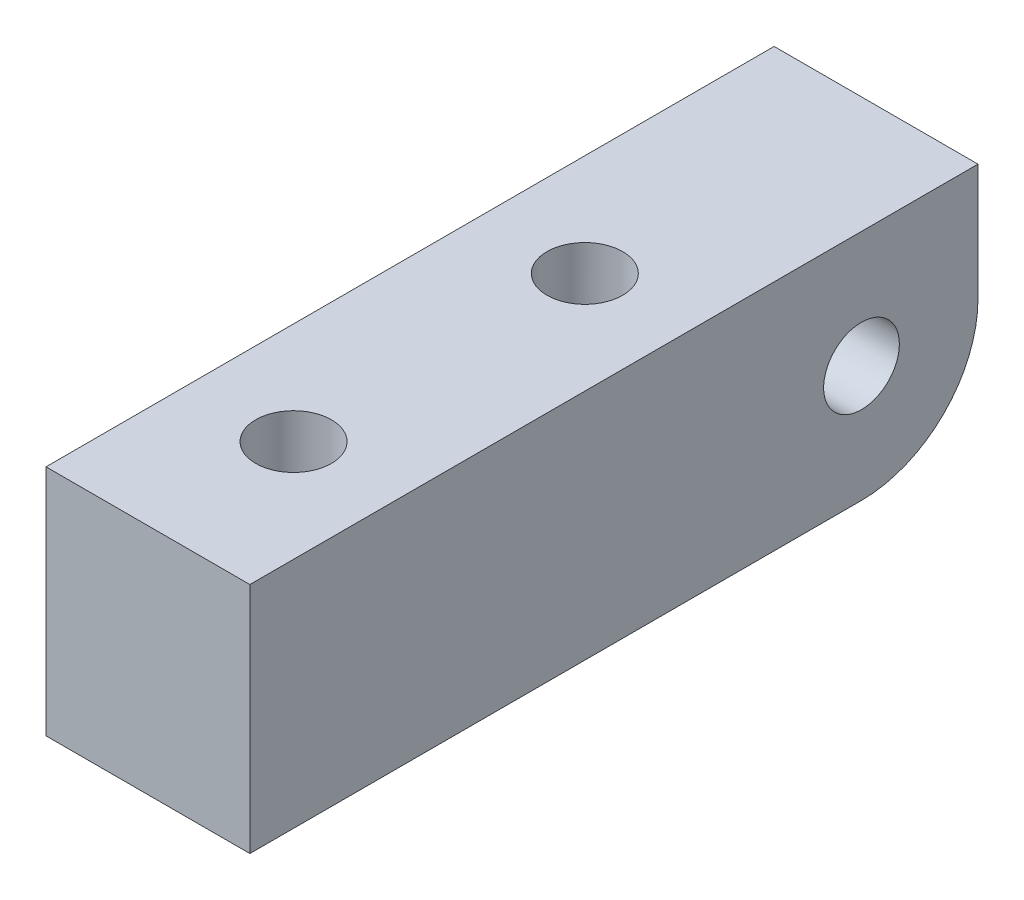
SolidWorks part; units mm, degrees
ref_plane "Front Plane" through (0, 0, 0) normal (0, 0, 1) x (1, 0, 0)
ref_plane "Top Plane" through (0, 0, 0) normal (0, 1, 0) x (1, 0, 0)
ref_plane "Right Plane" through (0, 0, 0) normal (1, 0, 0) x (0, 0, -1)
sketch "Sketch1" plane through (0, 0, 0) normal (1, 0, 0) x (0, 0, -1)
  line L0 (-4, 4) -> (-4, -4) construction
  line L1 (4, 4) -> (-21, 4)
  line L2 (4, 4) -> (4, -4)
  line L3 (4, -4) -> (-21, -4)
  line L4 (-21, 4) -> (-21, -4)
  line L5 (-7.3, 4) -> (-4.7, 4)
  line L6 (-7.3, 4) -> (-7.3, -4)
  line L7 (-7.3, -4) -> (-4.7, -4)
  line L8 (-4.7, 4) -> (-4.7, -4)
  line L9 (-4.7, 0) -> (-7.3, 0) construction
  line L11 (-6, 1.3) -> (-6, -1.5166) construction
  circle A0 centre (0, 0) radius 1.3
  circle A1 centre (0, 0) radius 4
  dimension "D1" = 2.6
  dimension "D2" = 8
  dimension "D3" = 2.6
  dimension "D4" = 10
  dimension "D5" = 25
  dimension "D6" = 1.3
extrude "Boss-Extrude1" add sketch "Sketch1" along normal mid plane 7 contours A1 A0 | A1 L2 L1 | L1 L0 A1 | L0 L1 L8 L3 | L8 L1 L6 L3 | L6 L1 L4 L3 | A1 L0 L3
sketch "Sketch3" plane through (0, 4, 0) normal (0, 1, 0) x (1, 0, 0)
  line L4 (3.5, 4) -> (-3.5, 4) construction
  circle A0 centre (0, -6) radius 1.3
  circle A3 centre (0, -16) radius 1.3
  dimension "D1" = 2.6
  dimension "D2" = 10
  dimension "D3" = 10
fillet "Fillet1" radius 4 1 edges at (0, -4, -4)
extrude "Cut-Extrude6" cut sketch "Sketch3" against normal through all
sketch "Sketch5" plane through (0, -4, 0) normal (0, -1, 0) x (1, 0, 0)
  circle A0 centre (0, 16) radius 2.5
  circle A1 centre (0, 6) radius 2.5
  dimension "D1" = 5
extrude "Cut-Extrude7" cut sketch "Sketch5" against normal blind 3
